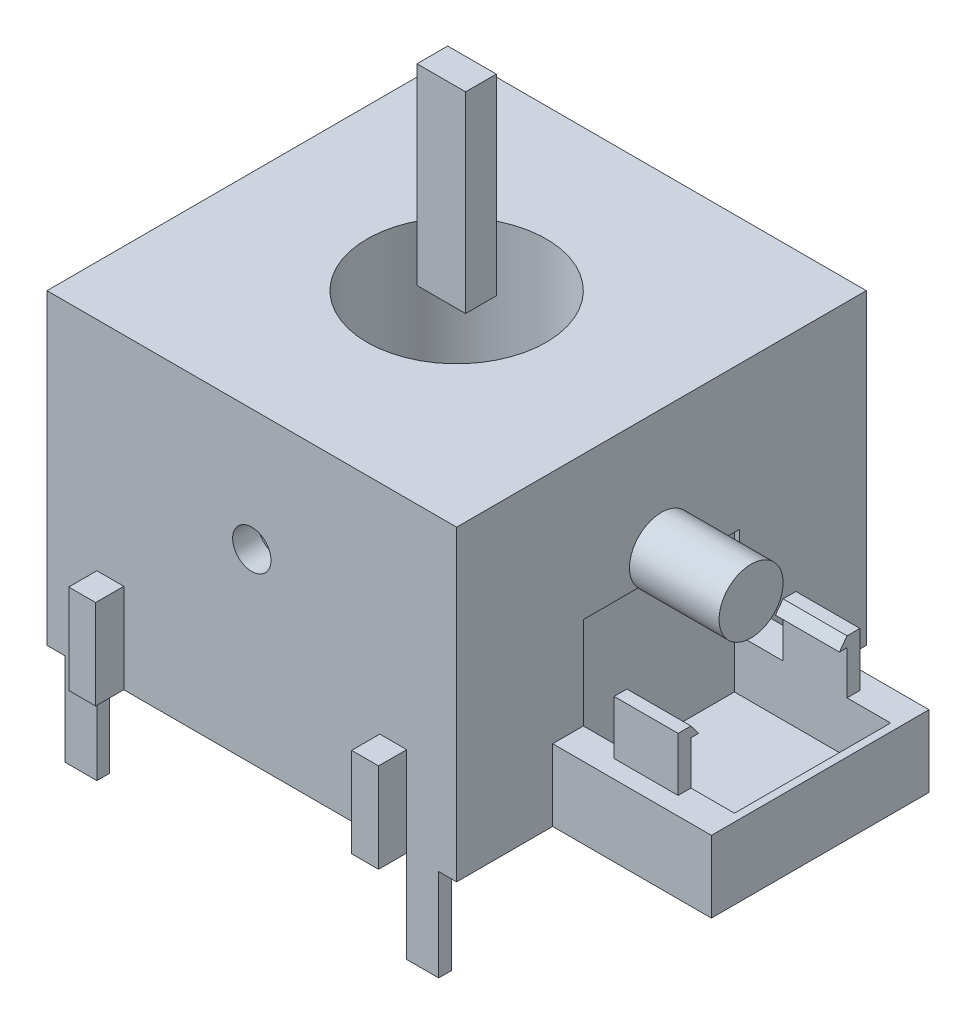
SolidWorks part; units mm, degrees
ref_plane "Plan de face" through (0, 0, 0) normal (0, 0, 1) x (1, 0, 0)
ref_plane "Plan de dessus" through (0, 0, 0) normal (0, 1, 0) x (1, 0, 0)
ref_plane "Plan de droite" through (0, 0, 0) normal (1, 0, 0) x (0, 0, -1)
sketch "Esquisse1" plane through (0, 0, 0) normal (0, 1, 0) x (1, 0, 0)
  line L1 (-8, -8) -> (8, -8)
  line L2 (-8, -8) -> (-8, 8)
  line L3 (-8, 8) -> (8, 8)
  line L4 (8, -8) -> (8, 8)
  line L5 (-8, -8) -> (8, 8) construction
  line L6 (-8, 8) -> (8, -8) construction
  circle A0 centre (0, 0) radius 3.5
  point P0 (0, 0)
  dimension "D1" = 16
extrude "Boss.-Extru.1" add sketch "Esquisse1" along normal blind 12
sketch "Esquisse2" plane through (0, 0, 0) normal (0, -1, 0) x (1, 0, 0)
  line L0 (-8, 8) -> (8, 8) construction
  line L1 (8, -8) -> (-8, -8) construction
  line L2 (-7.3, 8) -> (-6.05, 8)
  line L3 (-7.3, 8) -> (-7.3, 7.5)
  line L4 (-7.3, 7.5) -> (-6.05, 7.5)
  line L5 (-6.05, 8) -> (-6.05, 7.5)
  line L6 (7.3, 8) -> (6.05, 8)
  line L7 (7.3, 8) -> (7.3, 7.5)
  line L8 (7.3, 7.5) -> (6.05, 7.5)
  line L9 (6.05, 8) -> (6.05, 7.5)
  line L10 (7.3, -8) -> (6.05, -8)
  line L11 (7.3, -8) -> (7.3, -7.5)
  line L12 (7.3, -7.5) -> (6.05, -7.5)
  line L13 (6.05, -8) -> (6.05, -7.5)
  line L14 (-6.05, 8) -> (6.05, 8) construction
  line L15 (-7.3, -8) -> (-6.05, -8)
  line L16 (-7.3, -8) -> (-7.3, -7.5)
  line L17 (-7.3, -7.5) -> (-6.05, -7.5)
  line L18 (-6.05, -8) -> (-6.05, -7.5)
  line L19 (0, 8) -> (0, 0) construction
  dimension "D1" = 14.6
  dimension "D2" = 1.25
  dimension "D3" = 0.5
extrude "Boss.-Extru.2" add sketch "Esquisse2" along normal blind 3.6
sketch "Esquisse5" plane through (0, 0, 8) normal (0, 0, 1) x (1, 0, 0)
  line L0 (-8, 12) -> (8, 12) construction
  circle A0 centre (0, 7.25) radius 0.75
  dimension "D2" = 1.5
  dimension "D1" = 4.75
extrude "Enlèv. mat.-Extru.2" cut sketch "Esquisse5" against normal blind 1
sketch "Esquisse6" plane through (0, 0, 0) normal (0, -1, 0) x (1, 0, 0)
  line L0 (8, 8) -> (8, -8) construction
  line L1 (8, 4.25) -> (14.2, 4.25)
  line L2 (8, 4.25) -> (8, -4.25)
  line L3 (8, -4.25) -> (14.2, -4.25)
  line L4 (14.2, 4.25) -> (14.2, -4.25)
  line L5 (8, 0) -> (0, 0) construction
  dimension "D1" = 8.5
  dimension "D2" = 6.2
extrude "Boss.-Extru.4" add sketch "Esquisse6" against normal blind 2.8
sketch "Esquisse7" plane through (0, 2.8, 0) normal (0, 1, 0) x (1, 0, 0)
  line L0 (14.2, 0) -> (13.9, 0) construction
  line L1 (13.9, -3.05) -> (7.8, -3.05)
  line L2 (13.9, -3.05) -> (13.9, 3.05)
  line L3 (13.9, 3.05) -> (7.8, 3.05)
  line L4 (7.8, -3.05) -> (7.8, 3.05)
  line L5 (14.2, 4.25) -> (14.2, -4.25) construction
  dimension "D1" = 6.1
  dimension "D2" = 0.3
extrude "Enlèv. mat.-Extru.3" cut sketch "Esquisse7" against normal blind 2 and the other way blind 3.6
sketch "Esquisse3" plane through (8, 0, 0) normal (-1, 0, 0) x (0, 0, 1)
  line L2 (8, 12) -> (-8, 12) construction
  circle A0 centre (0, 7.25) radius 1.25
  dimension "D2" = 2.5
  dimension "D1" = 4.75
extrude "Boss.-Extru.3" add sketch "Esquisse3" against normal blind 3.5
sketch "Esquisse9" plane through (14.2, 0, 0) normal (1, 0, 0) x (0, 0, -1)
  line L0 (-3.05, 2.8) -> (-3.05, 4.5)
  line L1 (-3.05, 6.4) -> (-3.05, 2.8) construction
  line L2 (-3.05, 4.5) -> (-2.75, 4.5)
  line L3 (-2.75, 4.5) -> (-3.05, 4.9)
  line L4 (-3.05, 4.9) -> (-3.55, 4.9)
  line L5 (-3.55, 4.9) -> (-3.55, 2.8)
  line L6 (4.25, 2.8) -> (-4.25, 2.8) construction
  line L7 (-3.55, 2.8) -> (-3.05, 2.8)
  line L9 (-3.05, 0.8) -> (3.05, 0.8) construction
  dimension "D1" = 0.3
  dimension "D2" = 0.4
  dimension "D3" = 0.5
  dimension "D4" = 3.7
extrude "Boss.-Extru.5" add sketch "Esquisse9" against normal blind 2.5 from offset 2 offset against normal yes
mirror "Symétrie1" about plane through (0, 0, 0) normal (0, 0, 1) of "Boss.-Extru.5"
sketch "Esquisse10" plane through (0, 0, 8) normal (0, 0, 1) x (1, 0, 0)
  line L1 (-6.05, 0) -> (-5, 0)
  line L2 (-6.05, 0) -> (-6.05, 3.5)
  line L3 (-6.05, 3.5) -> (-5, 3.5)
  line L4 (-5, 0) -> (-5, 3.5)
  line L5 (6.05, 0) -> (5, 0)
  line L6 (6.05, 0) -> (6.05, 3.5)
  line L7 (6.05, 3.5) -> (5, 3.5)
  line L8 (5, 0) -> (5, 3.5)
  dimension "D1" = 3.5
  dimension "D2" = 10
extrude "Boss.-Extru.6" add sketch "Esquisse10" along normal blind 1.1
sketch "Esquisse11" plane through (0, 12, 0) normal (0, 1, 0) x (1, 0, 0)
  line L1 (-0.95, -0.6) -> (0.95, -0.6)
  line L2 (-0.95, -0.6) -> (-0.95, 0.6)
  line L3 (-0.95, 0.6) -> (0.95, 0.6)
  line L4 (0.95, -0.6) -> (0.95, 0.6)
  line L5 (-0.95, -0.6) -> (0.95, 0.6) construction
  line L6 (-0.95, 0.6) -> (0.95, -0.6) construction
  point P0 (0, 0)
  dimension "D1" = 1.9
  dimension "D2" = 1.2
extrude "Boss.-Extru.7" add sketch "Esquisse11" along normal blind 7.5 separate body
